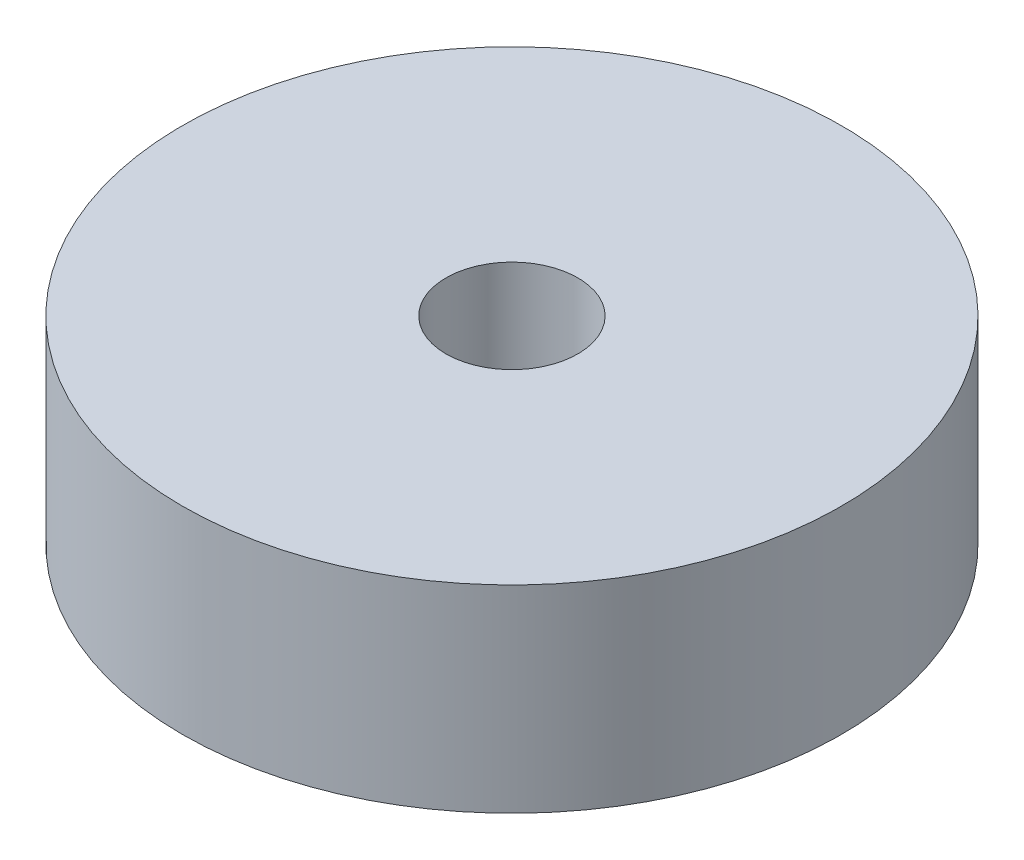
SolidWorks part; units mm, degrees
ref_plane "Front Plane" through (0, 0, 0) normal (0, 0, 1) x (1, 0, 0)
ref_plane "Top Plane" through (0, 0, 0) normal (0, 1, 0) x (1, 0, 0)
ref_plane "Right Plane" through (0, 0, 0) normal (1, 0, 0) x (0, 0, -1)
sketch "Sketch3" plane through (0, 0, 0) normal (0, 1, 0) x (1, 0, 0)
  line L0 (0, -55) -> (0, 55) construction
  circle A0 centre (0, 0) radius 10
  circle A1 centre (0, 0) radius 2
  point P0 (0, 0)
  dimension "D1" = 20
  dimension "D2" = 4
extrude "Boss-Extrude2" add sketch "Sketch3" along normal blind 6
